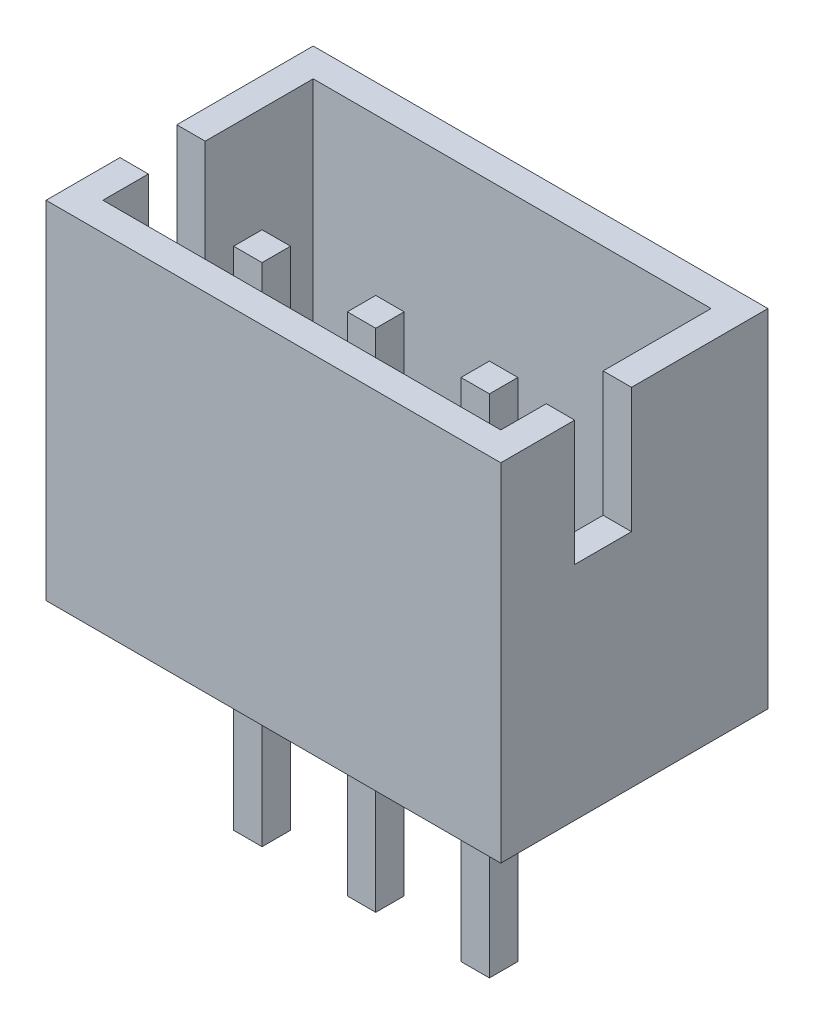
SolidWorks part; units mm, degrees
ref_plane "Front Plane" through (0, 0, 0) normal (0, 0, 1) x (1, 0, 0)
ref_plane "Top Plane" through (0, 0, 0) normal (0, 1, 0) x (1, 0, 0)
ref_plane "Right Plane" through (0, 0, 0) normal (1, 0, 0) x (0, 0, -1)
sketch "Sketch1" plane through (0, 0, 0) normal (0, 1, 0) x (1, 0, 0)
  line L1 (4, -2.35) -> (-4, -2.35)
  line L2 (4, -2.35) -> (4, 2.35)
  line L3 (4, 2.35) -> (-4, 2.35)
  line L4 (-4, -2.35) -> (-4, 2.35)
  line L5 (4, -2.35) -> (-4, 2.35) construction
  line L6 (4, 2.35) -> (-4, -2.35) construction
  point P0 (0, 0)
  dimension "D1" = 4.7
  dimension "D2" = 8
extrude "Boss-Extrude1" add sketch "Sketch1" along normal blind 6.1
shell "Shell1" thickness 0.5
sketch "Sketch2" plane through (0, 0.5, 0) normal (0, 1, 0) x (1, 0, 0)
  line L0 (-3.5, -0.55) -> (3.5, -0.55) construction
  line L1 (-3.5, 1.85) -> (-3.5, -1.85) construction
  line L2 (3.5, -1.85) -> (3.5, 1.85) construction
  line L3 (-4, -2.35) -> (4, -2.35) construction
  line L4 (0.25, -0.8) -> (0.25, -0.3)
  line L5 (-1.75, -0.8) -> (-2.25, -0.8)
  line L6 (-1.75, -0.8) -> (-1.75, -0.3)
  line L7 (-1.75, -0.3) -> (-2.25, -0.3)
  line L8 (-2.25, -0.8) -> (-2.25, -0.3)
  line L9 (-1.75, -0.8) -> (-2.25, -0.3) construction
  line L10 (-1.75, -0.3) -> (-2.25, -0.8) construction
  line L11 (0.25, -0.8) -> (-0.25, -0.8)
  line L12 (-0.25, -0.8) -> (-0.25, -0.3)
  line L13 (0.25, -0.3) -> (-0.25, -0.3)
  line L14 (2.25, -0.8) -> (2.25, -0.3)
  line L15 (2.25, -0.8) -> (1.75, -0.8)
  line L16 (1.75, -0.8) -> (1.75, -0.3)
  line L17 (2.25, -0.3) -> (1.75, -0.3)
  line L18 (-1.75, -0.8) -> (0.25, -0.8) construction
  point P8 (-2, -0.55)
  point P13 (0, -0.3)
  dimension "D1" = 1.8
  dimension "D2" = 0.5
  dimension "D4" = 2
  dimension "D3" = 3
extrude "Boss-Extrude2" add sketch "Sketch2" along normal blind 5 and the other way blind 3.9 separate body
sketch "Sketch3" plane through (-4, 0, 0) normal (-1, 0, 0) x (0, 0, 1)
  line L0 (-2.35, 6.1) -> (2.35, 6.1) construction
  line L1 (1.05, 3.9) -> (0.05, 3.9)
  line L2 (1.05, 3.9) -> (1.05, 6.1)
  line L3 (1.05, 6.1) -> (0.05, 6.1)
  line L4 (0.05, 3.9) -> (0.05, 6.1)
  line L5 (1.05, 3.9) -> (0.05, 6.1) construction
  line L6 (1.05, 6.1) -> (0.05, 3.9) construction
  line L7 (-2.35, 0) -> (2.35, 0) construction
  line L8 (0.3, -3.4) -> (0.8, -3.4) construction
  point P0 (0.55, 5)
  point P9 (0, 0)
  point P12 (0.55, -3.4)
  dimension "D1" = 5
  dimension "D2" = 1
extrude "Cut-Extrude1" cut sketch "Sketch3" against normal up to surface (7.5 mm away)
mirror "Mirror1" about plane through (0, 0, 0) normal (1, 0, 0) of "Cut-Extrude1"
